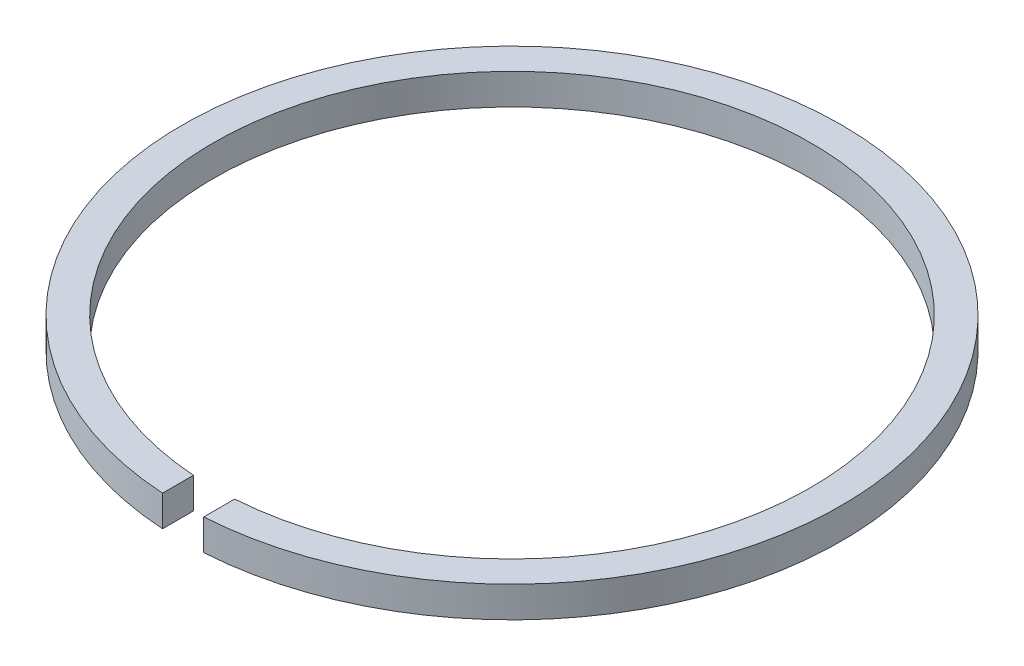
SolidWorks part; units mm, degrees
ref_plane "Front Plane" through (0, 0, 0) normal (0, 0, 1) x (1, 0, 0)
ref_plane "Top Plane" through (0, 0, 0) normal (0, 1, 0) x (1, 0, 0)
ref_plane "Right Plane" through (0, 0, 0) normal (1, 0, 0) x (0, 0, -1)
sketch "Sketch2" plane through (0, 0, 0) normal (0, 1, 0) x (1, 0, 0)
  line L0 (-1, -15.9687) -> (-1, -14.4655)
  line L1 (1, -15.9687) -> (1, -14.4655)
  arc A0 (-1, -15.9687) -> (1, -15.9687) centre (0, 0) cw
  arc A1 (1, -14.4655) -> (-1, -14.4655) centre (0, 0) ccw
  dimension "D4" = 14.5
  dimension "D1" = 16
  dimension "D2" = 2
  dimension "D3" = 1
extrude "Boss-Extrude1" add sketch "Sketch2" along normal mid plane 1.5
